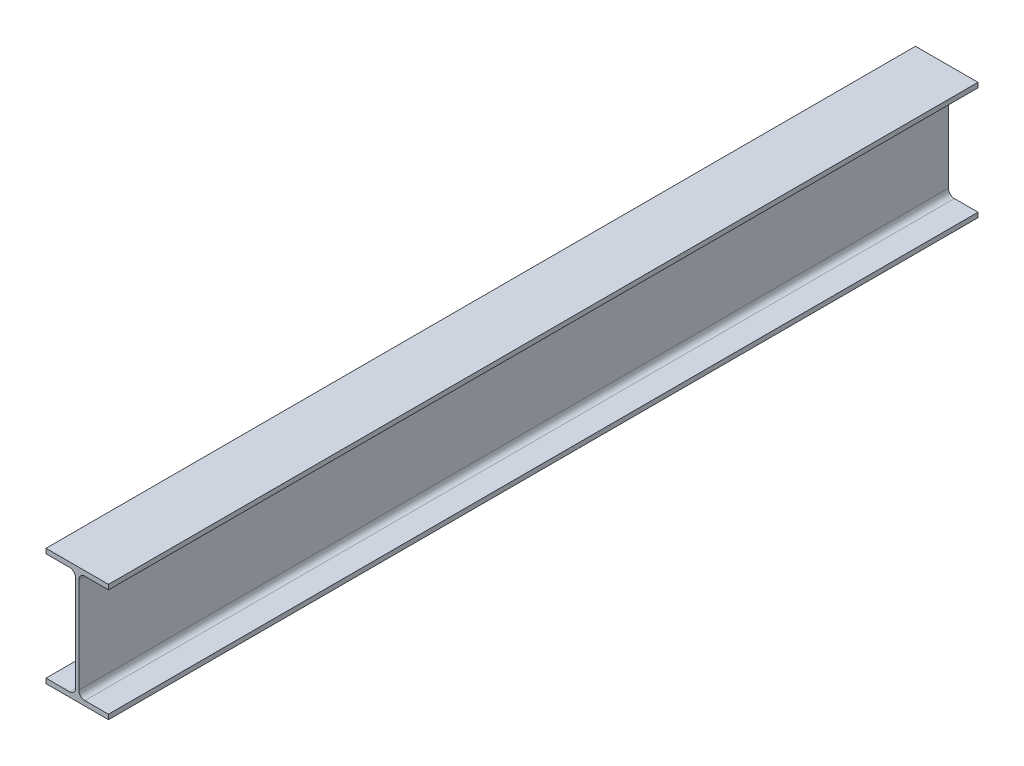
SolidWorks part; units mm, degrees
material "1.0035 (S185)"
ref_plane "Front Plane" through (0, 0, 0) normal (0, 0, 1) x (1, 0, 0)
ref_plane "Top Plane" through (0, 0, 0) normal (0, 1, 0) x (1, 0, 0)
ref_plane "Right Plane" through (0, 0, 0) normal (1, 0, 0) x (0, 0, -1)
sketch "Sketch1" plane through (0, 0, 0) normal (0, 0, 1) x (1, 0, 0)
  line L0 (-36.5, 14.0965) -> (36.5, 14.0965)
  line L1 (36.5, 14.0965) -> (36.5, 8.4965)
  line L2 (36.5, 8.4965) -> (8.9, 8.4965)
  line L3 (1.9, 1.4965) -> (1.9, -110.3035)
  line L4 (8.9, -117.3035) -> (36.5, -117.3035)
  line L5 (36.5, -117.3035) -> (36.5, -122.9035)
  line L6 (36.5, -122.9035) -> (-36.5, -122.9035)
  line L7 (-36.5, -122.9035) -> (-36.5, -117.3035)
  line L8 (-36.5, -117.3035) -> (-8.9, -117.3035)
  line L9 (-1.9, -110.3035) -> (-1.9, 1.4965)
  line L10 (-8.9, 8.4965) -> (-36.5, 8.4965)
  line L11 (-36.5, 8.4965) -> (-36.5, 14.0965)
  line L12 (-45.4222, -54.3557) -> (49.6039, -54.3557) construction
  arc A0 (8.9, -117.3035) -> (1.9, -110.3035) centre (8.9, -110.3035) cw
  arc A1 (-1.9, -110.3035) -> (-8.9, -117.3035) centre (-8.9, -110.3035) cw
  arc A2 (-8.9, 8.4965) -> (-1.9, 1.4965) centre (-8.9, 1.4965) cw
  arc A3 (1.9, 1.4965) -> (8.9, 8.4965) centre (8.9, 1.4965) cw
  dimension "D8" = 7
  dimension "D2" = 3.8
  dimension "D3" = 5.6
  dimension "D4" = 5.6
  dimension "D5" = 1.9
  dimension "D6" = 73
  dimension "D7" = 34.6
  dimension "D1" = 137
extrude "Boss-Extrude1" add sketch "Sketch1" along normal blind 1016
sketch "Sketch3" plane through (0, 14.0965, 0) normal (0, 1, 0) x (1, 0, 0)
  line L0 (-36.5, -1016) -> (-36.5, 0) construction
  line L1 (36.5, 0) -> (-36.5, 0)
  line L2 (36.5, 0) -> (36.5, -50)
  line L3 (36.5, -50) -> (-36.5, -50)
  line L4 (-36.5, 0) -> (-36.5, -50)
  dimension "D1" = 50
split line "Split Line3" [suppressed]
equation "\"D4@Sketch1\"=\"D3@Sketch1\""
equation "\"D5@Sketch1\"=\"D2@Sketch1\"/2"
equation "\"D7@Sketch1\"=(\"D6@Sketch1\"-\"D2@Sketch1\")/2"
